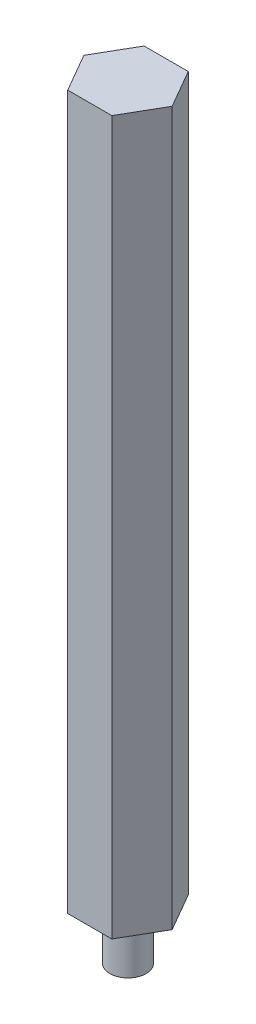
SolidWorks part; units mm, degrees
material "5052-H32"
ref_plane "Front Plane" through (0, 0, 0) normal (0, 0, 1) x (1, 0, 0)
ref_plane "Top Plane" through (0, 0, 0) normal (0, 1, 0) x (1, 0, 0)
ref_plane "Right Plane" through (0, 0, 0) normal (1, 0, 0) x (0, 0, -1)
sketch "Sketch1" plane through (0, 0, 0) normal (0, 1, 0) x (1, 0, 0)
  line L1 (7.3323, 0) -> (3.6662, 6.35)
  line L2 (3.6662, 6.35) -> (-3.6662, 6.35)
  line L3 (-3.6662, 6.35) -> (-7.3323, 0)
  line L4 (-7.3323, 0) -> (-3.6662, -6.35)
  line L5 (-3.6662, -6.35) -> (3.6662, -6.35)
  line L6 (3.6662, -6.35) -> (7.3323, 0)
  circle A0 centre (0, 0) radius 6.35 construction
extrude "Boss-Extrude1" add sketch "Sketch1" along normal blind 127
sketch "Sketch3" plane through (0, 0, 0) normal (0, -1, 0) x (1, 0, 0)
  circle A0 centre (0, 0) radius 3
  circle A1 centre (0, 0) radius 18.3116
  dimension "D1" = 6
  dimension "D2" = 36.6232
extrude "Cut-Extrude1" cut sketch "Sketch3" against normal blind 8.5
